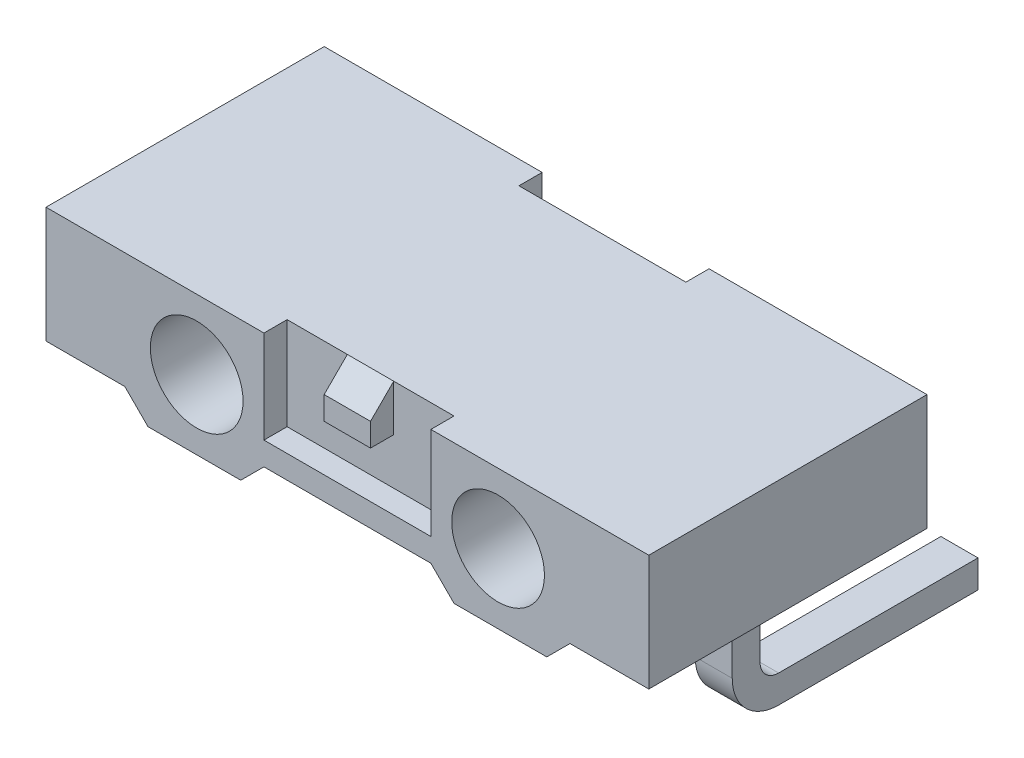
SolidWorks part; units mm, degrees
ref_plane "Piano frontale" through (0, 0, 0) normal (0, 0, 1) x (1, 0, 0)
ref_plane "Piano superiore" through (0, 0, 0) normal (0, 1, 0) x (1, 0, 0)
ref_plane "Piano destro" through (0, 0, 0) normal (1, 0, 0) x (0, 0, -1)
sketch "Schizzo1" plane through (0, 0, 0) normal (0, 0, 1) x (1, 0, 0)
  line L1 (-6.5, -1.25) -> (6.5, -1.25)
  line L2 (-6.5, -1.25) -> (-6.5, 1.25)
  line L3 (-6.5, 1.25) -> (6.5, 1.25)
  line L4 (6.5, -1.25) -> (6.5, 1.25)
  line L5 (-6.5, -1.25) -> (6.5, 1.25) construction
  line L6 (-6.5, 1.25) -> (6.5, -1.25) construction
  point P0 (0, 0)
  dimension "D1" = 13
  dimension "D2" = 2.5
extrude "Estrusione-Estrusione1" add sketch "Schizzo1" along normal mid plane 6
sketch "Schizzo2" plane through (0, 0, 3) normal (0, 0, 1) x (1, 0, 0)
  line L0 (-4.8, -1.25) -> (-4.3, -1.75)
  line L1 (-6.5, -1.25) -> (6.5, -1.25) construction
  line L2 (-4.3, -1.75) -> (-2.3, -1.75)
  line L3 (-2.3, -1.75) -> (-1.8, -1.25)
  line L4 (1.8, -1.25) -> (2.3, -1.75)
  line L5 (2.3, -1.75) -> (4.3, -1.75)
  line L6 (4.3, -1.75) -> (4.8, -1.25)
  line L8 (-4.8, -1.25) -> (-4.8, -0.938)
  line L9 (-4.8, -0.938) -> (4.8, -0.938)
  line L10 (4.8, -0.938) -> (4.8, -1.25)
  line L11 (1.8, -1.25) -> (-1.8, -1.25)
  dimension "D1" = 2
  dimension "D2" = 2
  dimension "D3" = 0.5
  dimension "D4" = 135
  dimension "D5" = 135
  dimension "D6" = 135
  dimension "D7" = 135
  dimension "D8" = 3.6
  dimension "D9" = 1.7
extrude "Estrusione-Estrusione2" add sketch "Schizzo2" against normal up to surface (6 mm away) up to face at (0, 0, -3)
sketch "Schizzo3" plane through (0, 0, 3) normal (0, 0, 1) x (1, 0, 0)
  line L0 (-4.3, -1.75) -> (-2.3, -1.75) construction
  circle A0 centre (-3.25, -0.25) radius 1
  circle A1 centre (3.25, -0.25) radius 1
  dimension "D1" = 2
  dimension "D4" = 0.5
  dimension "D2" = 6.5
  dimension "D3" = 3.25
extrude "Taglio-Estrusione1" cut sketch "Schizzo3" against normal through all
sketch "Schizzo4" plane through (0, 0, 3) normal (0, 0, 1) x (1, 0, 0)
  line L0 (6.5, 1.25) -> (-6.5, 1.25) construction
  line L1 (-1.8, 1.25) -> (-0.5011, 1.25)
  line L2 (-1.8, 1.25) -> (-1.8, -0.75)
  line L3 (-1.8, -0.75) -> (1.8, -0.75)
  line L4 (1.8, 1.25) -> (1.8, -0.75)
  line L5 (0.4989, 1.25) -> (1.8, 1.25)
  line L7 (-0.5011, 1.25) -> (-0.5011, 0.25)
  line L8 (-0.5011, 0.25) -> (0.4989, 0.25)
  line L9 (0.4989, 1.25) -> (0.4989, 0.25)
  dimension "D1" = 3.6
  dimension "D2" = 2
  dimension "D3" = 1.8
  dimension "D4" = 1
  dimension "D5" = 1.2989
  dimension "D6" = 1
extrude "Taglio-Estrusione2" cut sketch "Schizzo4" against normal blind 0.5
mirror "Specchia2" about plane through (0, 0, 0) normal (0, 0, 1) of "Taglio-Estrusione2"
chamfer "Smusso1" distance 0.5 angle 45 2 edges at (-0.0011, 1.25, 3) (-0.0011, 1.25, -3)
sketch "Schizzo5" plane through (0, 0, 0) normal (1, 0, 0) x (0, 0, -1)
  line L0 (0, -1.25) -> (0, -2.85) construction
  line L1 (-3, -1.25) -> (3, -1.25) construction
  line L2 (0.7, -3.55) -> (5, -3.55) construction
  line L3 (-0.3, -1.25) -> (-0.3, -2.85)
  line L4 (0.7, -3.85) -> (5, -3.85)
  line L5 (0.3, -1.25) -> (0.3, -2.85)
  line L6 (0.7, -3.25) -> (5, -3.25)
  line L7 (-0.3, -1.25) -> (0.3, -1.25)
  line L8 (5, -3.85) -> (5, -3.25)
  arc A0 (0.7, -3.55) -> (0, -2.85) centre (0.7, -2.85) cw construction
  arc A1 (0.7, -3.85) -> (-0.3, -2.85) centre (0.7, -2.85) cw
  arc A2 (0.7, -3.25) -> (0.3, -2.85) centre (0.7, -2.85) cw
  point P8 (0, -3.55)
  dimension "D3" = 0.7
  dimension "D1" = 2.3
  dimension "D2" = 5
  dimension "D4" = 0.3
  dimension "D5" = 0.3
extrude "Estrusione-Estrusione3" add sketch "Schizzo5" along normal mid plane 0.8
pattern_linear "Ripetizione a L1" count 2 spacing 5.2 along (-1, 0, 0) count 2 spacing 5.2 along (1, 0, 0) of "Estrusione-Estrusione3"
